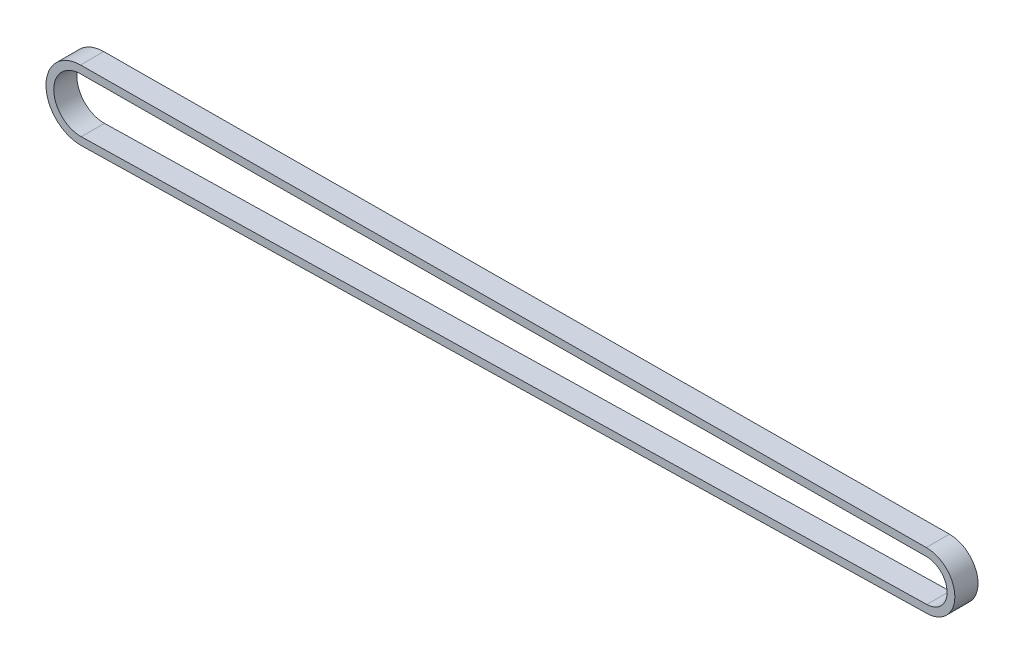
SolidWorks part; units mm, degrees
ref_plane "Front Plane" through (0, 0, 0) normal (0, 0, 1) x (1, 0, 0)
ref_plane "Top Plane" through (0, 0, 0) normal (0, 1, 0) x (1, 0, 0)
ref_plane "Right Plane" through (0, 0, 0) normal (1, 0, 0) x (0, 0, -1)
sketch "Sketch1" plane through (0, 0, 0) normal (0, 0, 1) x (1, 0, 0)
  line L0 (-108.7177, 6.3594) -> (110.2919, 7.6404)
  line L1 (110.435, -3.0654) -> (-108.5306, -7.639)
  line L2 (110.4768, -5.065) -> (-108.4888, -9.6386)
  line L3 (-108.7294, 8.3593) -> (110.2802, 9.6404)
  arc A0 (-108.5306, -7.639) -> (-108.7177, 6.3594) centre (-108.6768, -0.6405) cw
  arc A1 (110.2919, 7.6404) -> (110.435, -3.0654) centre (110.3232, 2.287) cw
  arc A2 (110.2802, 9.6404) -> (110.4768, -5.065) centre (110.3232, 2.287) cw
  arc A3 (-108.4888, -9.6386) -> (-108.7294, 8.3593) centre (-108.6768, -0.6405) cw
  dimension "D1" = 2
extrude "Boss-Extrude1" add sketch "Sketch1" along normal blind 6
